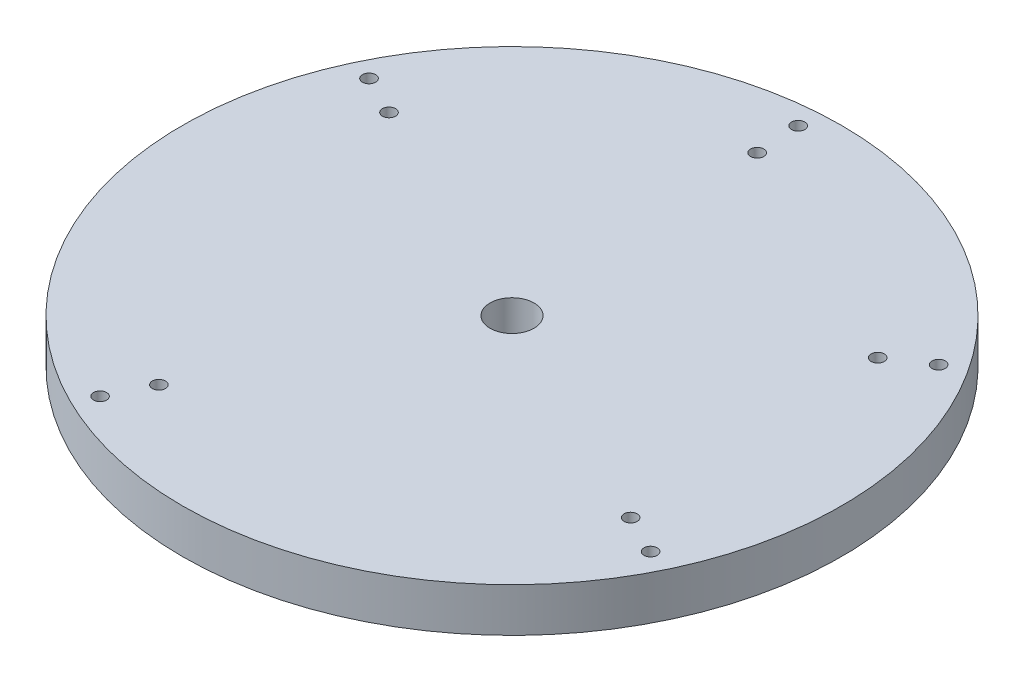
SolidWorks part; units mm, degrees
ref_plane "Front Plane" through (0, 0, 0) normal (0, 0, 1) x (1, 0, 0)
ref_plane "Top Plane" through (0, 0, 0) normal (0, 1, 0) x (1, 0, 0)
ref_plane "Right Plane" through (0, 0, 0) normal (1, 0, 0) x (0, 0, -1)
sketch "Sketch1" plane through (0, 0, 0) normal (0, 1, 0) x (1, 0, 0)
  circle A0 centre (0, 0) radius 75
  circle A1 centre (0, 0) radius 5
  dimension "D1" = 150
  dimension "D2" = 10
extrude "Boss-Extrude1" add sketch "Sketch1" along normal blind 10
sketch "Sketch4" plane through (0, 10, 0) normal (0, 1, 0) x (1, 0, 0)
  line L0 (0, 0) -> (-44.3556, -89.8874) construction
  line L1 (0, 0) -> (86.9898, -42.9257) construction
  line L2 (0, 0) -> (93.1903, 62.234) construction
  line L3 (0, 0) -> (-6.6466, 101.7982) construction
  line L4 (0, 0) -> (-87.1109, 42.9855) construction
  circle A0 centre (-26.5508, -53.8057) radius 1.5
  circle A1 centre (-30.9759, -62.7733) radius 1.5
  circle A2 centre (-63.0151, 30.4803) radius 1.5
  circle A3 centre (-54.0475, 26.0551) radius 1.5
  circle A6 centre (62.2777, -30.7342) radius 1.5
  circle A7 centre (53.31, -26.309) radius 1.5
  circle A8 centre (30.2385, 62.5194) radius 1.5 [skipped]
  circle A9 centre (25.8134, 53.5518) radius 1.5 [skipped]
  circle A12 centre (-4.8536, 69.9788) radius 1.5
  circle A13 centre (-4.202, 60) radius 1.5
  circle A14 centre (-58.5079, -38.515) radius 1.5 [skipped]
  circle A15 centre (-50.1918, -32.9614) radius 1.5 [skipped]
  circle A16 centre (0, 0) radius 75 construction
  circle A17 centre (49.8965, 33.3217) radius 1.5
  circle A18 centre (58.2126, 38.8753) radius 1.5
  point P13 (-33.1885, -67.2571)
  point P26 (-0.3687, -0.127)
  point P35 (-0.3613, 0.2432)
  dimension "D5" = 3
  dimension "D6" = 3
  dimension "D7" = 10
  dimension "D10" = 60
  dimension "D13" = 3
  dimension "D14" = 3
  dimension "D15" = 10
  dimension "D1" = 90
  dimension "D2" = 60
  dimension "D3" = 60
  dimension "D4" = 90
  dimension "D11" = 60
  dimension "D12" = 60
  dimension "D16" = 60
  dimension "D8" = 4
  dimension "D9" = 3
extrude "Cut-Extrude1" cut sketch "Sketch4" against normal through all both and the other way through all
